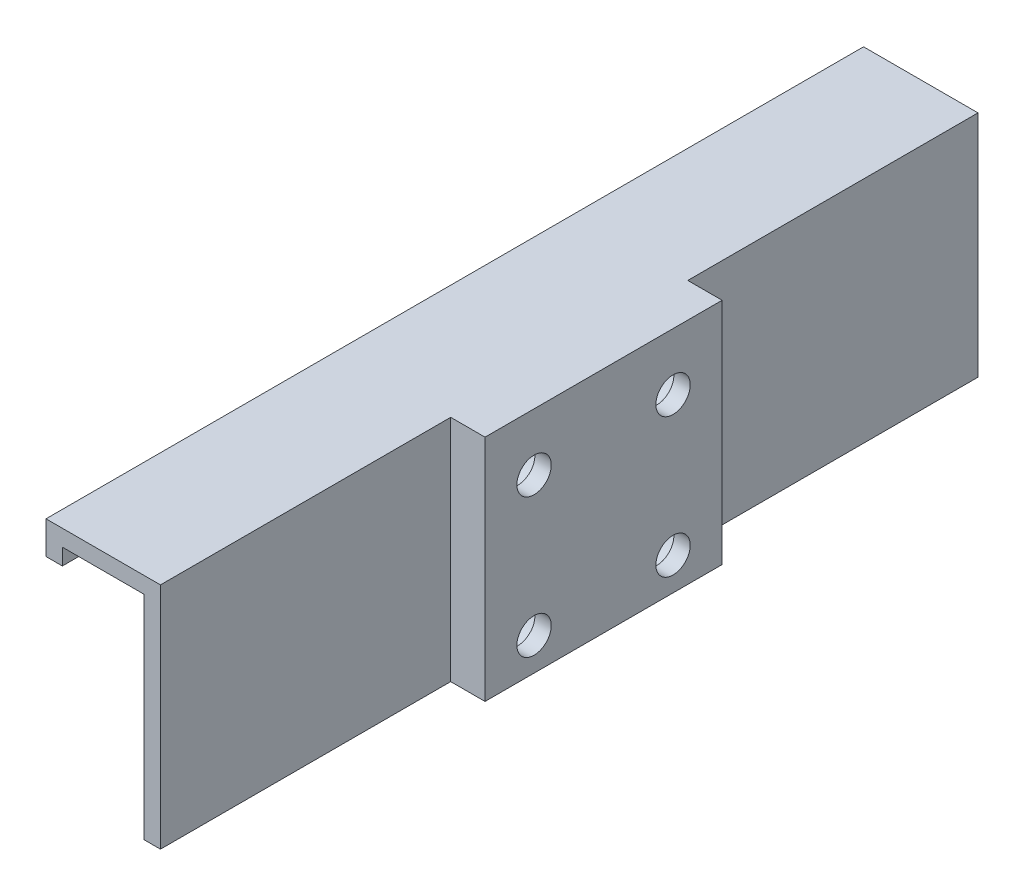
SolidWorks part; units mm, degrees
ref_plane "Front Plane" through (0, 0, 0) normal (0, 0, 1) x (1, 0, 0)
ref_plane "Top Plane" through (0, 0, 0) normal (0, 1, 0) x (1, 0, 0)
ref_plane "Right Plane" through (0, 0, 0) normal (1, 0, 0) x (0, 0, -1)
sketch "Sketch1" plane through (0, 0, 0) normal (1, 0, 0) x (0, 0, -1)
  line L1 (0, 0) -> (100, 0)
  line L2 (0, 0) -> (0, 26)
  line L3 (0, 26) -> (100, 26)
  line L4 (100, 0) -> (100, 26)
  dimension "D1" = 100
  dimension "D2" = 26
extrude "Boss-Extrude1" add sketch "Sketch1" along normal blind 2
sketch "Sketch2" plane through (0, 0, 0) normal (0, 0, 1) x (1, 0, 0)
  line L0 (2, 26) -> (2, 28)
  line L1 (2, 28) -> (-12, 28)
  line L2 (-12, 28) -> (-12, 24)
  line L3 (-12, 24) -> (-10, 24)
  line L4 (-10, 24) -> (-10, 26)
  line L5 (-10, 26) -> (2, 26)
  line L6 (2, 0) -> (0, 0) construction
  line L7 (0, 26) -> (0, 0) construction
  dimension "D1" = 10
  dimension "D2" = 2
extrude "Boss-Extrude2" add sketch "Sketch2" against normal up to surface (100 mm away) up to face at (1, 13, -100)
sketch "Sketch3" plane through (2, 0, 0) normal (1, 0, 0) x (0, 0, -1)
  line L0 (100, 28) -> (0, 28) construction
  line L1 (37.5, 28) -> (62.5, 28)
  line L2 (37.5, 28) -> (37.5, 0)
  line L3 (37.5, 0) -> (62.5, 0)
  line L4 (62.5, 28) -> (62.5, 0)
  line L5 (0, 0) -> (100, 0) construction
  point P8 (50, 0)
  point P9 (50, 28)
  dimension "D1" = 25
  dimension "D2" = 28
extrude "Boss-Extrude3" add sketch "Sketch3" along normal blind 4
sketch "Sketch4" plane through (6, 0, 0) normal (1, 0, 0) x (0, 0, -1)
  line L0 (62.5, 28) -> (37.5, 28) construction
  line L1 (41.5, 21) -> (58.5, 21) construction
  line L2 (41.5, 21) -> (41.5, 4) construction
  line L3 (41.5, 4) -> (58.5, 4) construction
  line L4 (58.5, 21) -> (58.5, 4) construction
  line L5 (37.5, 28) -> (37.5, 0) construction
  line L6 (37.5, 25) -> (62.5, 25) construction
  line L7 (37.5, 25) -> (37.5, 0) construction
  line L8 (37.5, 0) -> (62.5, 0) construction
  line L9 (62.5, 25) -> (62.5, 0) construction
  circle A0 centre (41.5, 21) radius 2.1
  circle A1 centre (58.5, 21) radius 2.1
  circle A2 centre (58.5, 4) radius 2.1
  circle A3 centre (41.5, 4) radius 2.1
  point P6 (50, 28)
  point P7 (50, 21)
  point P15 (62.5, 12.5)
  point P16 (58.5, 12.5)
  dimension "D2" = 25
  dimension "D3" = 4.2
  dimension "D1" = 17
extrude "Cut-Extrude1" cut sketch "Sketch4" against normal through all
other "Move Face1" face at (4, 14, -37.5) face at (4, 14, -62.5) parameters "D1"=2
sketch "Sketch5" plane through (0, 0, 0) normal (-1, 0, 0) x (0, 0, 1)
  circle A0 centre (-58.5, 21) radius 3.6
  circle A1 centre (-41.5, 21) radius 3.6
  circle A2 centre (-41.5, 4) radius 3.6
  circle A3 centre (-58.5, 4) radius 3.6
  dimension "D1" = 7.2
extrude "Cut-Extrude2" cut sketch "Sketch5" against normal blind 4.2
other "Move Face2" face at (6, 4, -43.6) parameters "D1"=4
other "Move Face3" face at (10, 4, -43.6) parameters "D1"=3.8
